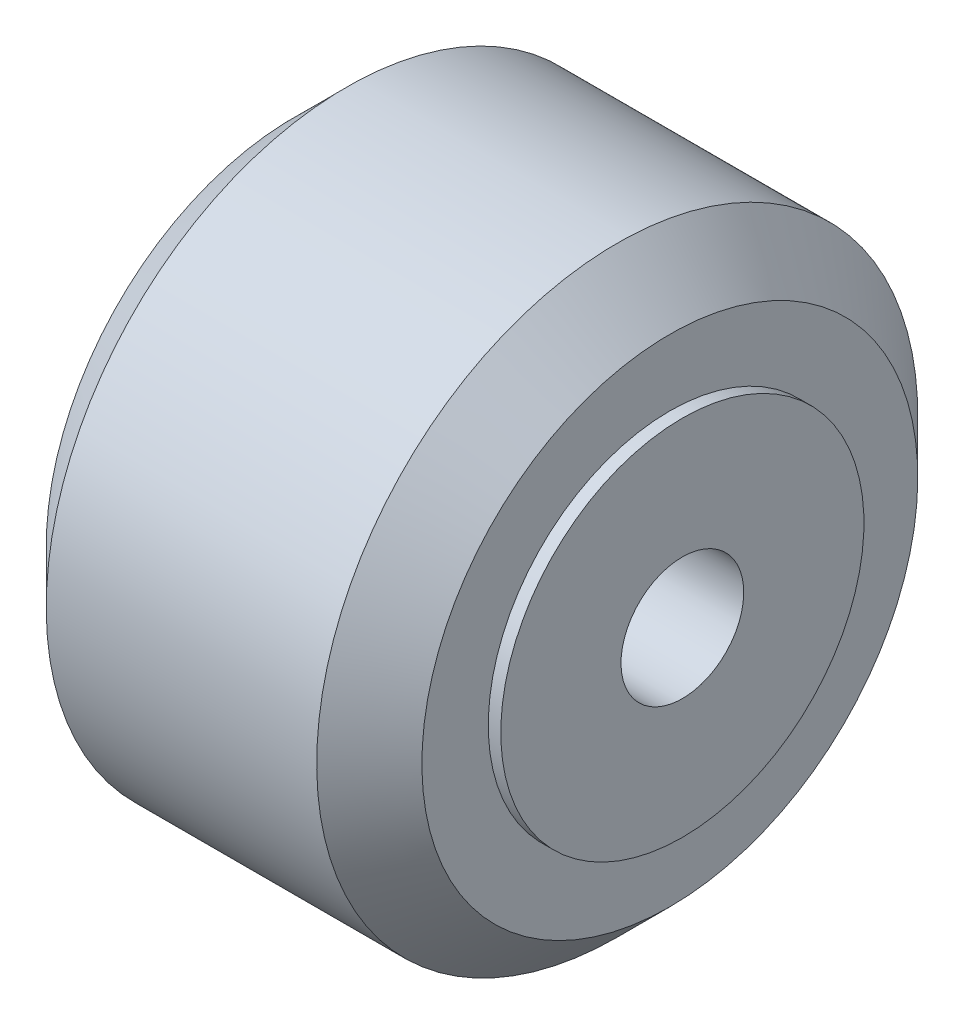
SolidWorks part; units mm, degrees
ref_plane "Alzado" through (0, 0, 0) normal (0, 0, 1) x (1, 0, 0)
ref_plane "Planta" through (0, 0, 0) normal (0, 1, 0) x (1, 0, 0)
ref_plane "Vista lateral" through (0, 0, 0) normal (1, 0, 0) x (0, 0, -1)
sketch "Croquis1" plane through (0, 0, 0) normal (0, 0, 1) x (1, 0, 0)
  line L0 (0, 0) -> (-3, 0) construction
  line L1 (-3, 0) -> (-3, 2.45) construction
  line L2 (-5.4, 12) -> (5.4, 12)
  line L5 (0, 12) -> (0, 0) construction
  line L6 (-5.4, 12) -> (-7.5, 9.9)
  line L10 (-3, 0) -> (-3, 2.45) construction
  line L11 (0, 0) -> (-3, 2.45) construction
  line L12 (3, 2.45) -> (7.5, 2.45)
  line L13 (0, 0) -> (-7.5, 0) construction
  line L14 (-7.5, 0) -> (-7.5, 9.9)
  line L15 (-3, 2.45) -> (3, 2.45)
  line L16 (-3, 2.45) -> (-7.5, 2.45)
  line L17 (7.5, 0) -> (7.5, 9.9)
  line L18 (5.4, 12) -> (7.5, 9.9)
  line L19 (0, 0) -> (7.5, 0) construction
  point P6 (0, 2.45)
  dimension "D1" = 15
  dimension "D3" = 45
  dimension "D4" = 9.9
  dimension "D5" = 12
revolve "Revolución1" add sketch "Croquis1" angle 360 about L19
sketch "Croquis2" plane through (7.5, 0, 0) normal (1, 0, 0) x (0, 0, -1)
  circle A0 centre (0, 0) radius 7.25
  circle A1 centre (0, 0) radius 2.45
  dimension "D1" = 14.5
extrude "Saliente-Extruir1" add sketch "Croquis2" along normal blind 0.5 and the other way blind 15.6 separate body contours A0 | A1
sketch "Croquis3" plane through (7.5, 0, 0) normal (1, 0, 0) x (0, 0, -1)
  circle A0 centre (0, 0) radius 7.25
extrude "Cortar-Extruir1" cut sketch "Croquis3" against normal blind 17.5 and the other way blind 14
